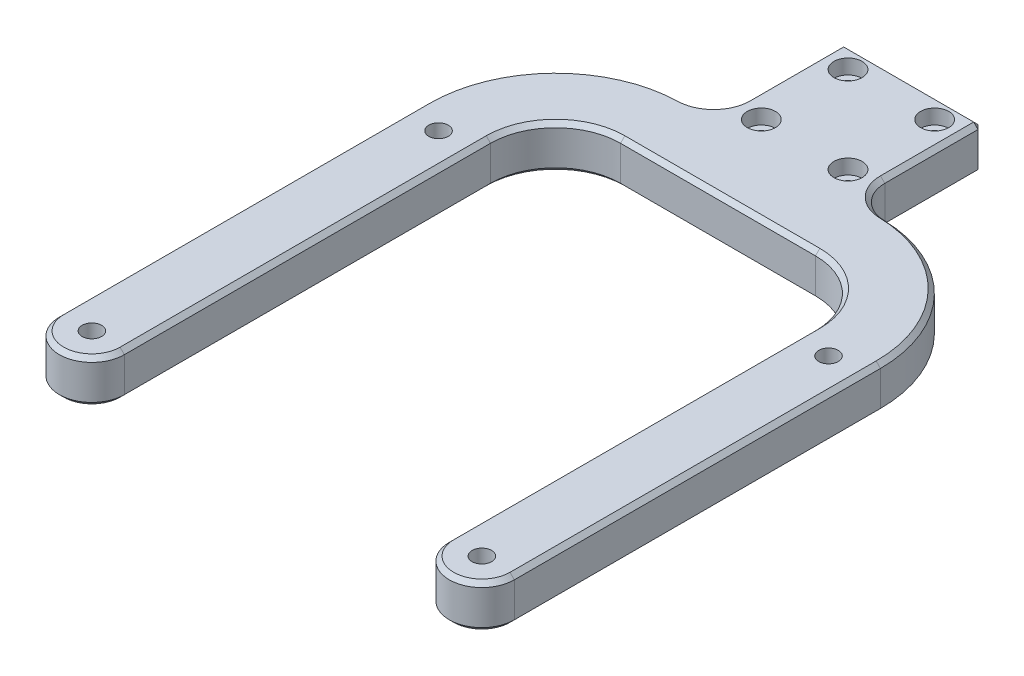
SolidWorks part; units mm, degrees
material "ABS PC"
ref_plane "Front Plane" through (0, 0, 0) normal (0, 0, 1) x (1, 0, 0)
ref_plane "Top Plane" through (0, 0, 0) normal (0, 1, 0) x (1, 0, 0)
ref_plane "Right Plane" through (0, 0, 0) normal (1, 0, 0) x (0, 0, -1)
sketch "Sketch1" plane through (0, 0, 0) normal (0, 1, 0) x (1, 0, 0)
  line L0 (22.5, 57.25) -> (0, 57.25)
  line L1 (0, 57.25) -> (0, 102.25)
  line L2 (37.5, 42.25) -> (37.5, -42.25)
  line L7 (16, 102.25) -> (0, 102.25)
  line L8 (0, 0) -> (0, 57.25) construction
  line L9 (16, 102.25) -> (16, 72.25)
  line L13 (16, 72.25) -> (22.5, 72.25)
  line L14 (52.5, 42.25) -> (52.5, -42.25)
  arc A4 (22.5, 57.25) -> (37.5, 42.25) centre (22.5, 42.25) cw
  arc A6 (22.5, 72.25) -> (52.5, 42.25) centre (22.5, 42.25) cw
  arc A9 (37.5, -42.25) -> (52.5, -42.25) centre (45, -42.25) ccw
  circle A10 centre (45, 37.75) radius 2.25
  circle A11 centre (45, -42.25) radius 2.25
  point P10 (37.5, 0)
  dimension "D7" = 80
  dimension "D8" = 30
  dimension "D9" = 15
  dimension "D6" = 107
  dimension "D14" = 4.5
  dimension "D1" = 15
  dimension "D2" = 15
  dimension "D3" = 30
  dimension "D4" = 32
  dimension "D5" = 75
extrude "Boss-Extrude1" add sketch "Sketch1" along normal blind 10 contours A6 L14 L2 A4 L0 L1 L7 L9 L13
fillet "Fillet1" radius 7.5 1 edges at (16, 5, -72.25)
chamfer "Chamfer1" distance 1 angle 45 19 edges at (11.25, 0, -57.25) (33.1066, 0, -52.8566) (37.5, 0, 0) (52.5, 0, 0) (43.9942, 0, -63.1784) (16, 0, -90.9933) (8, 0, -102.25) (11.25, 10, -57.25) (33.1066, 10, -52.8566) (37.5, 10, 0) (52.5, 10, 0) (43.9942, 10, -63.1784) (16, 10, -90.9933) (8, 10, -102.25) (18.1265, 0, -74.5046) (18.1265, 10, -74.5046) (16, 5, -102.25) (45, 0, 49.75) (45, 10, 49.75)
sketch "Sketch5" plane through (0, 0, 0) normal (0, -1, 0) x (1, 0, 0)
  circle A0 centre (45, -37.75) radius 2.25 construction
  circle A1 centre (45, 42.25) radius 2.25 construction
  circle A2 centre (45, -37.75) radius 2.25
  circle A3 centre (45, 42.25) radius 2.25
extrude "Boss-Extrude2" add sketch "Sketch5" against normal offset from surface (4 mm away) 6 up to face at (26.3251, 10, -47.0845)
mirror "Mirror1" about plane through (0, 10, -57.25) normal (1, 0, 0) of bodies 104 101
sketch "Sketch6" plane through (0, 10, 0) normal (0, 1, 0) x (1, 0, 0)
  line L0 (-15, 102.25) -> (15, 102.25) construction
  line L1 (-16, 102.25) -> (16, 102.25) construction
  line L2 (-16, 102.25) -> (-16, 72.25) construction
  line L3 (-16, 72.25) -> (16, 72.25) construction
  line L4 (16, 102.25) -> (16, 72.25) construction
  line L5 (16, 101.25) -> (16, 79.7367) construction
  line L7 (-10, 97.25) -> (10, 97.25) construction
  line L8 (-10, 97.25) -> (-10, 77.25) construction
  line L9 (-10, 77.25) -> (10, 77.25) construction
  line L10 (10, 97.25) -> (10, 77.25) construction
  circle A0 centre (10, 97.25) radius 1.5 construction
  circle A1 centre (10, 77.25) radius 1.5 construction
  circle A2 centre (-10, 97.25) radius 1.5 construction
  circle A3 centre (-10, 77.25) radius 1.5 construction
  dimension "D3" = 3
  dimension "D4" = 17
  dimension "D5" = 3.5
  dimension "D6" = 4.5
  dimension "D7" = 17
  dimension "D1" = 32
  dimension "D2" = 30
hole_wizard "CBORE for M3 Hex Socket Head Cap Screw1" positions "Sketch7" profile "Sketch8" counterbore size "M3" standard "ISO" end condition through all
sketch "Sketch7" plane through (0, 10, 0) normal (0, 1, 0) x (1, 0, 0)
  point P0 (10, 97.25)
  point P3 (-10, 97.25)
  point P6 (-10, 77.25)
  point P9 (10, 77.25)
  point P12 (0, 0)
sketch "Sketch8" plane through (10, 10, -97.25) normal (1, 0, 0) x (0, 0, 1)
  line L0 (0, 0) -> (0, 10)
  line L1 (0, 10) -> (1.7, 10)
  line L3 (1.7, 10) -> (1.7, 3.4)
  line L4 (1.7, 3.4) -> (3.25, 3.4)
  line L5 (3.25, 3.4) -> (3.25, 0)
  line L7 (3.25, 0) -> (0, 0)
  line L11 (0, -6.35) -> (0, 107.95) construction
  dimension "Thru Hole Dia." = 3.4
  dimension "Thru Hole Depth" = 10
  dimension "C'Bore Dia." = 6.5
  dimension "C'Bore Depth" = 3.4
